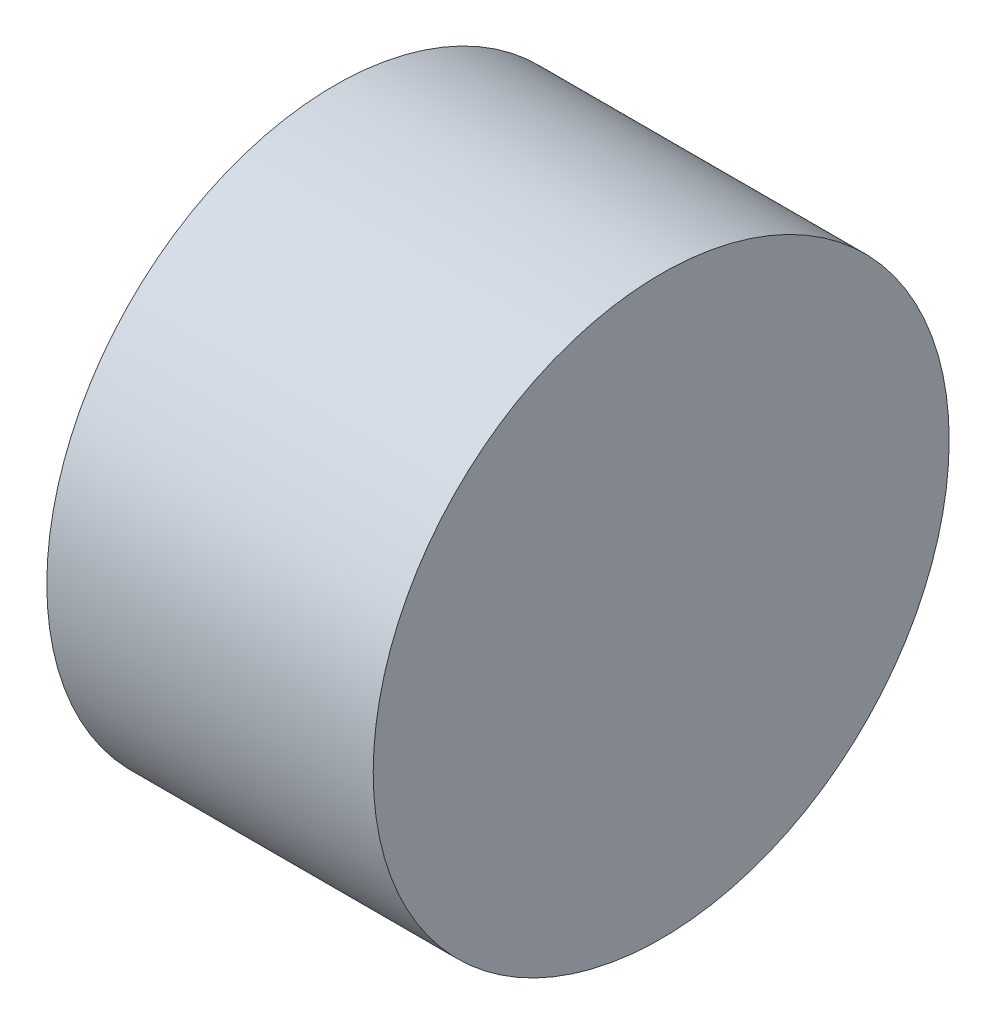
SolidWorks part; units mm, degrees
material "PTFE (general)"
ref_plane "Front" through (0, 0, 0) normal (0, 0, 1) x (1, 0, 0)
ref_plane "Top" through (0, 0, 0) normal (0, 1, 0) x (1, 0, 0)
ref_plane "Right" through (0, 0, 0) normal (1, 0, 0) x (0, 0, -1)
sketch "Sketch1" plane through (0, 0, 0) normal (0, 1, 0) x (1, 0, 0)
  line L0 (-21.462, 0) -> (19.3544, 0) construction
  line L1 (65, 0) -> (65, 75)
  line L2 (65, 75) -> (-20, 75)
  line L3 (-20, 75) -> (-20, 34.641)
  line L4 (40, 0) -> (65, 0)
  line L5 (-50, 0) -> (50, 0) construction
  line L6 (-20, 34.641) -> (0, 0) construction
  line L7 (0, 0) -> (40, 0) construction
  arc A0 (-20, 34.641) -> (40, 0) centre (0, 0) cw
  dimension "D2" = 120
  dimension "D3" = 40
  dimension "D4" = 85
  dimension "D1" = 75
revolve "Revolve7" add sketch "Sketch1" angle 360 about L0
